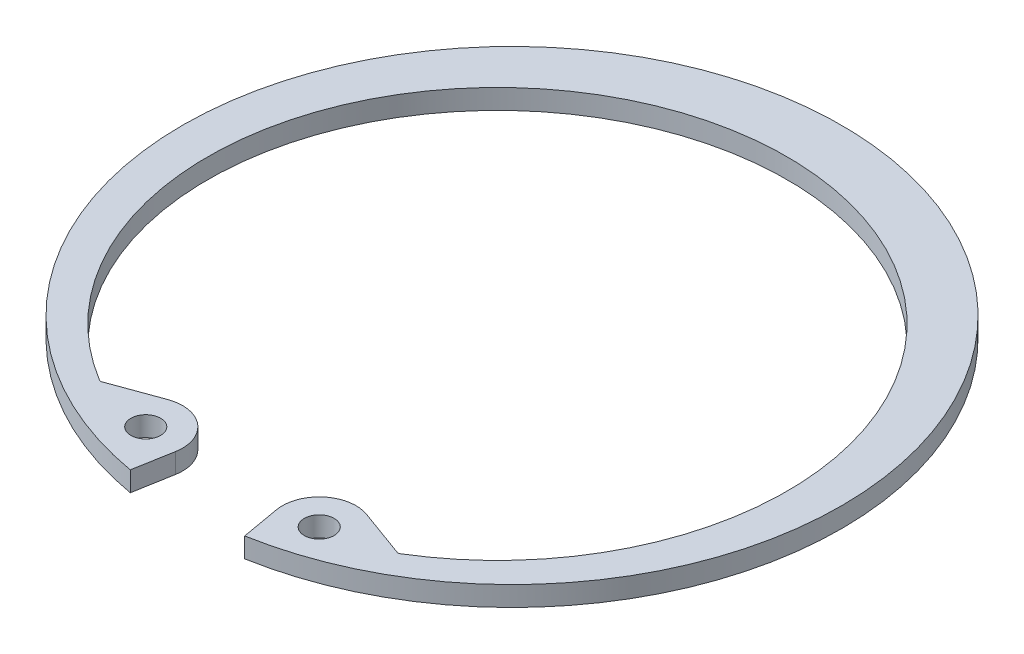
SolidWorks part; units mm, degrees
material "Cast Carbon Steel"
ref_plane "Front" through (0, 0, 0) normal (0, 0, 1) x (1, 0, 0)
ref_plane "Top" through (0, 0, 0) normal (0, 1, 0) x (1, 0, 0)
ref_plane "Right" through (0, 0, 0) normal (1, 0, 0) x (0, 0, -1)
sketch "Sketch2" plane through (0, 0, 0) normal (0, 1, 0) x (1, 0, 0)
  line L0 (0, 0) -> (0, -26.1112) construction
  line L1 (-11.8105, -20.838) -> (-12.8751, -22.7162) construction
  line L2 (4.5342, -25.7145) -> (3.9949, -22.656)
  line L3 (-4.5342, -25.7145) -> (-3.9949, -22.656)
  line L4 (0, 21.7932) -> (0, 26.1112) construction
  line L5 (11.8105, -20.838) -> (7.8705, -19.4039)
  line L6 (-11.8105, -20.838) -> (-7.8705, -19.4039)
  line L7 (6.006, -19.3589) -> (-6.3862, -23.2035) construction
  line L8 (-6.3862, -23.2035) -> (-4.6552, -28.7832) construction
  line L9 (-4.6552, -28.7832) -> (7.737, -24.9386) construction
  line L10 (6.006, -19.3589) -> (7.737, -24.9386) construction
  line L11 (6.8715, -22.1488) -> (3.9949, -22.656) construction
  line L12 (6.8715, -22.1488) -> (7.737, -24.9386) construction
  line L13 (6.006, -19.3589) -> (-6.006, -19.3589) construction
  line L14 (-6.006, -19.3589) -> (-7.737, -24.9386) construction
  line L15 (-26.1112, 0) -> (26.1112, 0) construction
  arc A1 (4.5342, -25.7145) -> (-4.5342, -25.7145) centre (0, 0) ccw
  arc A2 (11.8105, -20.838) -> (-11.8105, -20.838) centre (0, -1.1584) ccw
  circle A3 centre (0, 0) radius 26.1112 construction
  arc A4 (3.9949, -22.656) -> (7.8705, -19.4039) centre (6.8715, -22.1488) cw
  arc A5 (-3.9949, -22.656) -> (-7.8705, -19.4039) centre (-6.8715, -22.1488) ccw
  circle A6 centre (6.8715, -22.1488) radius 1.1811
  circle A7 centre (-6.8715, -22.1488) radius 1.1811
  arc A8 (11.8105, -20.838) -> (-11.8105, -20.838) centre (0, -1.1584) cw construction
  circle A9 centre (0, 0) radius 20.066 construction
  point P5 (6.8715, -22.1488)
  point P10 (6.006, -19.3589)
  dimension "D1" = 60
  dimension "D2" = 60
  dimension "L" = 40.132
  dimension "R" = 2.3622
  dimension "Df" = 52.2224
  dimension "H" = 5.842
  dimension "Angle" = 10
  dimension "Sec. Max" = 4.318
  dimension "Sec. Min" = 2.159
extrude "Extrude1" add sketch "Sketch2" against normal blind 1.5748
fillet "Fillet1" radius 0.254 2 edges at (-11.8105, -0.7874, 20.838) (11.8105, -0.7874, 20.838)
sketch "Sketch3" plane through (0, 0, 0) normal (1, 0, 0) x (0, 0, -1)
  line L0 (-24.6126, -16.4592) -> (-24.6126, -1.651)
  line L1 (-24.6126, -1.651) -> (-26.1112, -1.651)
  line L2 (-26.1112, -1.651) -> (-26.1112, 0.0762)
  line L3 (-26.1112, 0.0762) -> (-24.6126, 0.0762)
  line L4 (-24.6126, 0.0762) -> (-24.6126, 2.4384)
  line L5 (-24.6126, -16.4592) -> (-27.6098, -16.4592)
  line L6 (-24.6126, -1.651) -> (0, -1.651) construction
  line L7 (-24.6126, 2.4384) -> (-27.6098, 2.4384)
  line L8 (0, 130.3401) -> (0, 164.6301) construction
  line L9 (0, -1.651) -> (0, 0.0762) construction
  line L10 (0, 0.0762) -> (-24.6126, 0.0762) construction
  line L11 (-26.1112, -0.7874) -> (0, -0.7874) construction
  line L12 (0, -135.0899) -> (0, 130.3401) construction
  line L13 (-20.7748, -1.5748) -> (21.7932, -1.5748) construction
  line L14 (-27.6098, -16.4592) -> (-27.6098, 2.4384)
  dimension "Shaft Lg" = 18.8976
  dimension "D1" = 0.7874
  dimension "D2" = 1.4986
  dimension "D4" = 1.4986
  dimension "D3" = 2.3622
revolve "Revolve1" [suppressed] add sketch "Sketch3" angle 360 about L8
delete or keep bodies "Body-Delete1" [suppressed] type delete bodies bodies 116
equation "\"D3@Sketch3\" = \"Shaft Lg@Sketch3\"/8"
equation "\"Shaft Lg@Sketch3\" = \"D1@Extrude1\"*12"
equation "\"D1@Sketch3\" = \"D1@Extrude1\"/2"
equation "\"D2@Sketch3\" = \"D4@Sketch3\""
